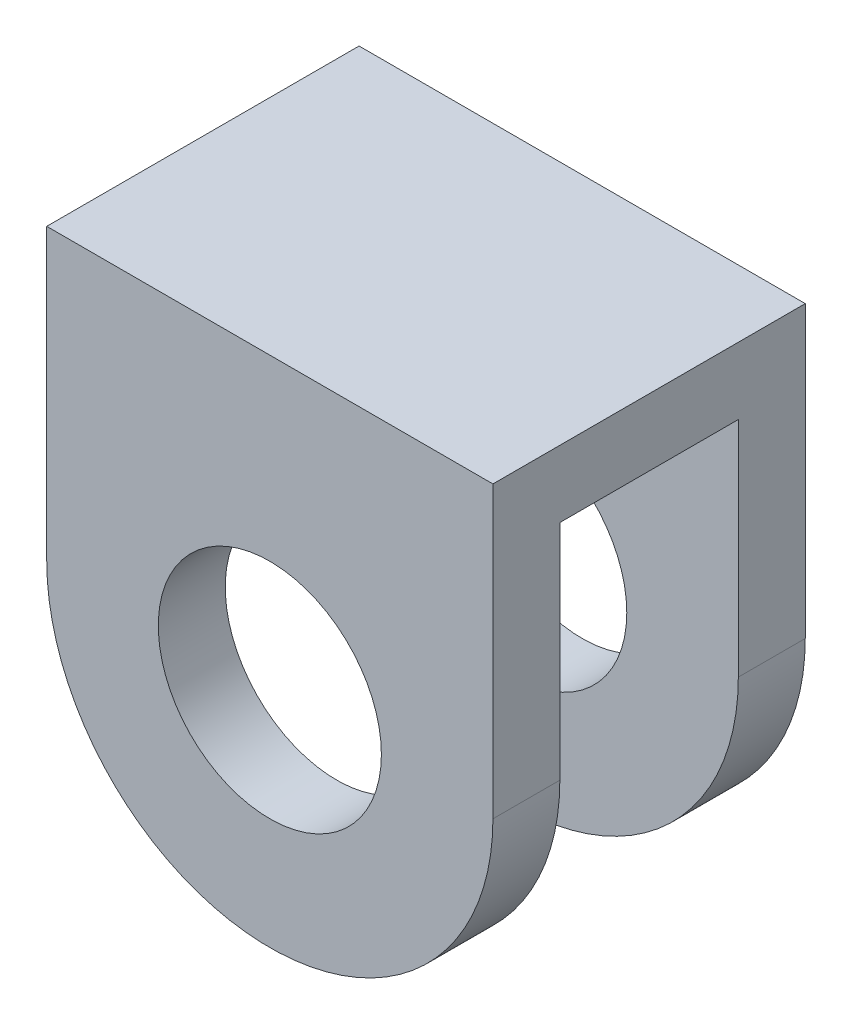
SolidWorks part; units mm, degrees
ref_plane "前视基准面" through (0, 0, 0) normal (0, 0, 1) x (1, 0, 0)
ref_plane "上视基准面" through (0, 0, 0) normal (0, 1, 0) x (1, 0, 0)
ref_plane "右视基准面" through (0, 0, 0) normal (1, 0, 0) x (0, 0, -1)
sketch "草图1" plane through (0, 0, 0) normal (0, 0, 1) x (1, 0, 0)
  line L0 (-35.6032, 55.5226) -> (-15.6032, 55.5226)
  line L1 (-15.6032, 55.5226) -> (-15.6032, 45.5226)
  line L3 (-35.6032, 45.5226) -> (-35.6032, 55.5226)
  line L4 (-25.6032, 35.5226) -> (-25.6032, 45.5226) construction
  circle A0 centre (-25.6032, 45.5226) radius 5
  arc A1 (-35.6032, 45.5226) -> (-15.6032, 45.5226) centre (-25.6032, 45.5226) ccw
extrude "凸台-拉伸1" add sketch "草图1" along normal blind 3
sketch "草图2" plane through (0, 55.5226, 0) normal (0, 1, 0) x (1, 0, 0)
  line L0 (-35.6032, -3) -> (-35.6032, 11)
  line L1 (-35.6032, 11) -> (-15.6032, 11)
  line L2 (-15.6032, 11) -> (-15.6032, -3)
  line L4 (-15.6032, -3) -> (-35.6032, -3)
extrude "凸台-拉伸2" add sketch "草图2" along normal blind 3
sketch "草图3" plane through (0, 58.5226, 0) normal (0, 1, 0) x (1, 0, 0)
  line L0 (-15.6032, 4) -> (-38.4813, 4) construction
  line L1 (-15.6032, -3) -> (-15.6032, 11) construction
ref_plane "基准面1" through (0, 0, -4) normal (0, 0, -1) x (-1, 0, 0)
mirror "镜向1" about plane through (0, 0, -4) normal (0, 0, -1) of "凸台-拉伸1"
